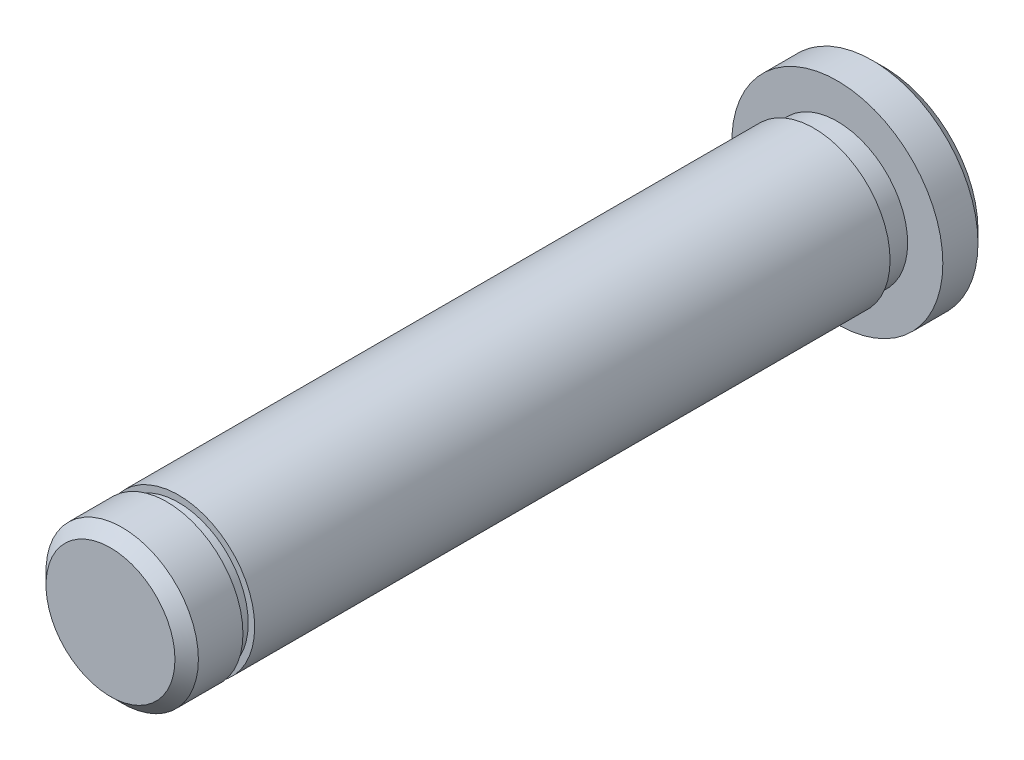
SolidWorks part; units mm, degrees
ref_plane "前视基准面" through (0, 0, 0) normal (0, 0, 1) x (1, 0, 0)
ref_plane "上视基准面" through (0, 0, 0) normal (0, 1, 0) x (1, 0, 0)
ref_plane "右视基准面" through (0, 0, 0) normal (1, 0, 0) x (0, 0, -1)
other "Configuration Table"
sketch "草图1" plane through (0, 0, 0) normal (0, 0, 1) x (1, 0, 0)
  circle A0 centre (0, 0) radius 9
  dimension "D1" = 18
extrude "凸台-拉伸1" add sketch "草图1" along normal blind 4
sketch "草图2" plane through (0, 0, 4) normal (0, 0, 1) x (1, 0, 0)
  circle A0 centre (0, 0) radius 6.5
  dimension "D1" = 13
extrude "凸台-拉伸2" add sketch "草图2" along normal blind 62
sketch "草图4" plane through (0, 0, 4) normal (0, 0, 1) x (1, 0, 0)
  circle A0 centre (0, 0) radius 6
  dimension "D1" = 12
extrude "切除-拉伸1" cut sketch "草图4" along normal blind 2 flip side to cut
sketch "草图5" plane through (0, 0, 66) normal (0, 0, 1) x (1, 0, 0)
  circle A0 centre (0, 0) radius 5.95
  dimension "D1" = 11.9
extrude "切除-拉伸2" cut sketch "草图5" along normal blind 1 from offset 5.8 flip side to cut offset against normal yes
chamfer "倒角1" distance 1 angle 45 2 edges at (6.5, 0, 66) (9, 0, 0)
